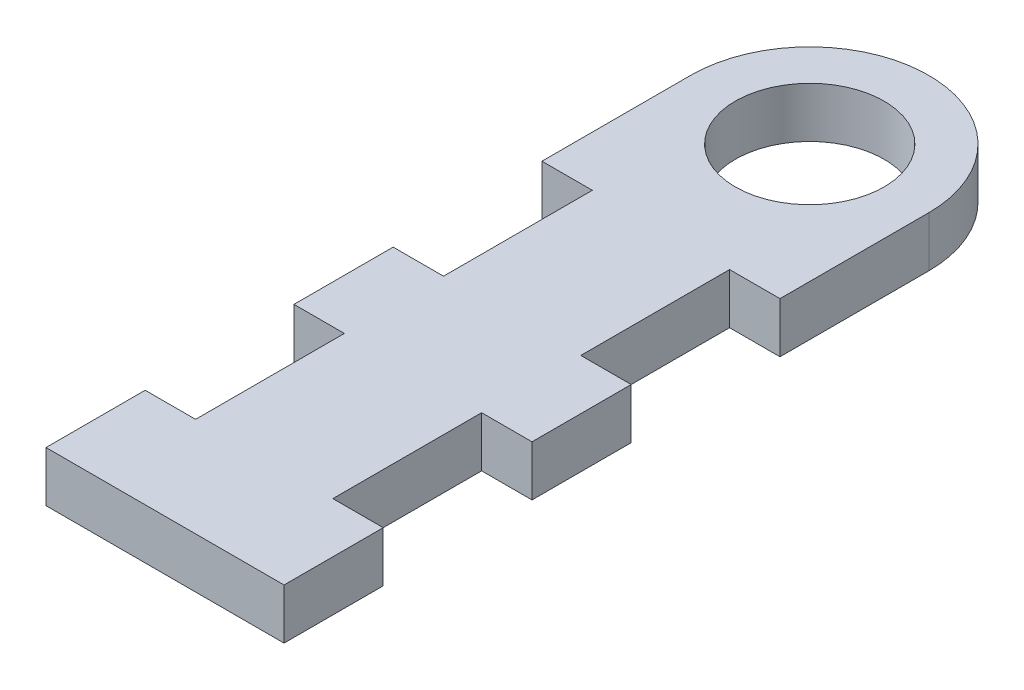
SolidWorks part; units mm, degrees
ref_plane "Front Plane" through (0, 0, 0) normal (0, 0, 1) x (1, 0, 0)
ref_plane "Top Plane" through (0, 0, 0) normal (0, 1, 0) x (1, 0, 0)
ref_plane "Right Plane" through (0, 0, 0) normal (1, 0, 0) x (0, 0, -1)
sketch "Sketch1" plane through (0, 0, 0) normal (0, 1, 0) x (1, 0, 0)
  line L0 (-12, 32.5) -> (12, 32.5) construction
  line L1 (12, -32.5) -> (-12, -32.5)
  line L2 (12, -32.5) -> (12, 32.5)
  line L4 (-12, -32.5) -> (-12, 32.5)
  line L5 (12, -32.5) -> (-12, 32.5) construction
  line L6 (12, 32.5) -> (-12, -32.5) construction
  arc A0 (12, 32.5) -> (-12, 32.5) centre (0, 32.5) ccw
  circle A1 centre (0, 32.5) radius 7.5
  point P0 (0, 0)
  dimension "D3" = 15
  dimension "D1" = 65
  dimension "D2" = 24
extrude "Boss-Extrude1" add sketch "Sketch1" along normal blind 5.08
sketch "Sketch2" plane through (0, 5.08, 0) normal (0, 1, 0) x (1, 0, 0)
  line L0 (-12, -32.5) -> (12, -32.5) construction
  line L1 (-12, 32.5) -> (-12, -32.5) construction
  line L15 (-12, -22.5) -> (-6.92, -22.5)
  line L16 (-12, -22.5) -> (-12, -7.5)
  line L17 (-12, -7.5) -> (-6.92, -7.5)
  line L18 (-6.92, -22.5) -> (-6.92, -7.5)
  line L19 (-12, 2.5) -> (-6.92, 2.5)
  line L20 (-12, 2.5) -> (-12, 17.5)
  line L21 (-12, 17.5) -> (-6.92, 17.5)
  line L22 (-6.92, 2.5) -> (-6.92, 17.5)
  dimension "D1" = 15
  dimension "D2" = 10
  dimension "D4" = 5.08
  dimension "D3" = 10
extrude "Cut-Extrude1" cut sketch "Sketch2" against normal up to surface (5.08 mm away) up to face at (0, 0, -3)
mirror "Mirror2" about plane through (0, 0, 0) normal (1, 0, 0) of "Cut-Extrude1"
